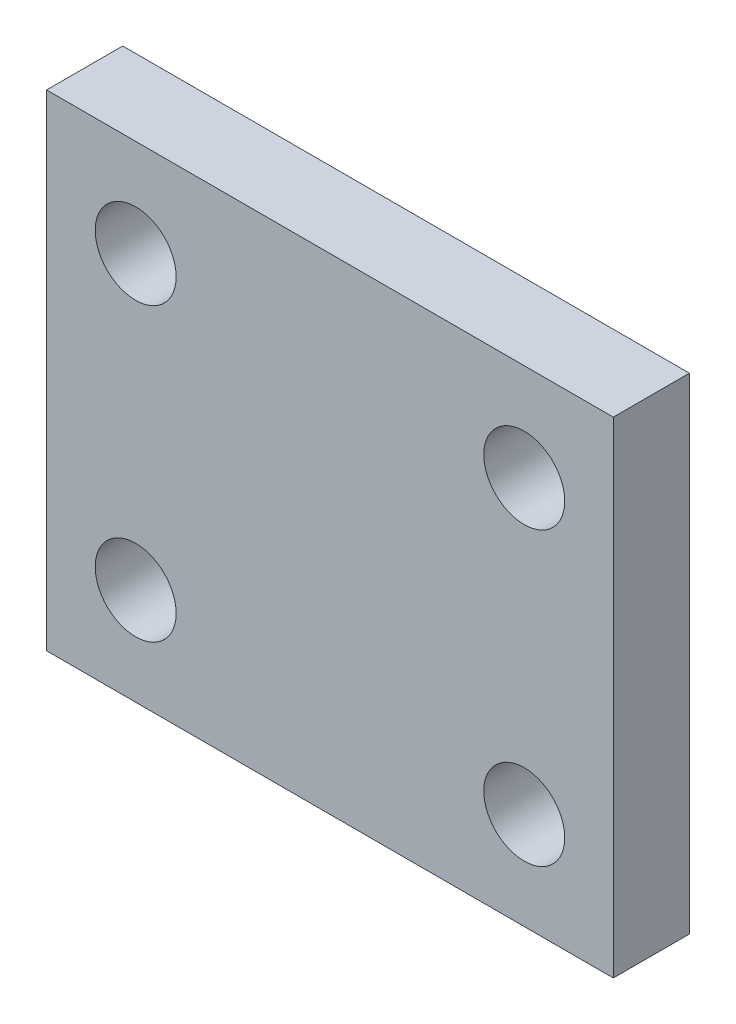
SolidWorks part; units mm, degrees
ref_plane "Front Plane" through (0, 0, 0) normal (0, 0, 1) x (1, 0, 0)
ref_plane "Top Plane" through (0, 0, 0) normal (0, 1, 0) x (1, 0, 0)
ref_plane "Right Plane" through (0, 0, 0) normal (1, 0, 0) x (0, 0, -1)
sketch "Sketch1" plane through (0, 0, 0) normal (0, 0, 1) x (1, 0, 0)
  line L1 (0, 0) -> (35, 0)
  line L2 (0, 0) -> (0, 30)
  line L3 (0, 30) -> (35, 30)
  line L4 (35, 0) -> (35, 30)
  circle A0 centre (5.5, 24) radius 2.5
  circle A1 centre (29.5, 24) radius 2.5
  circle A2 centre (5.5, 6) radius 2.5
  circle A3 centre (29.5, 6) radius 2.5
extrude "Boss-Extrude1" add sketch "Sketch1" along normal blind 4.7
